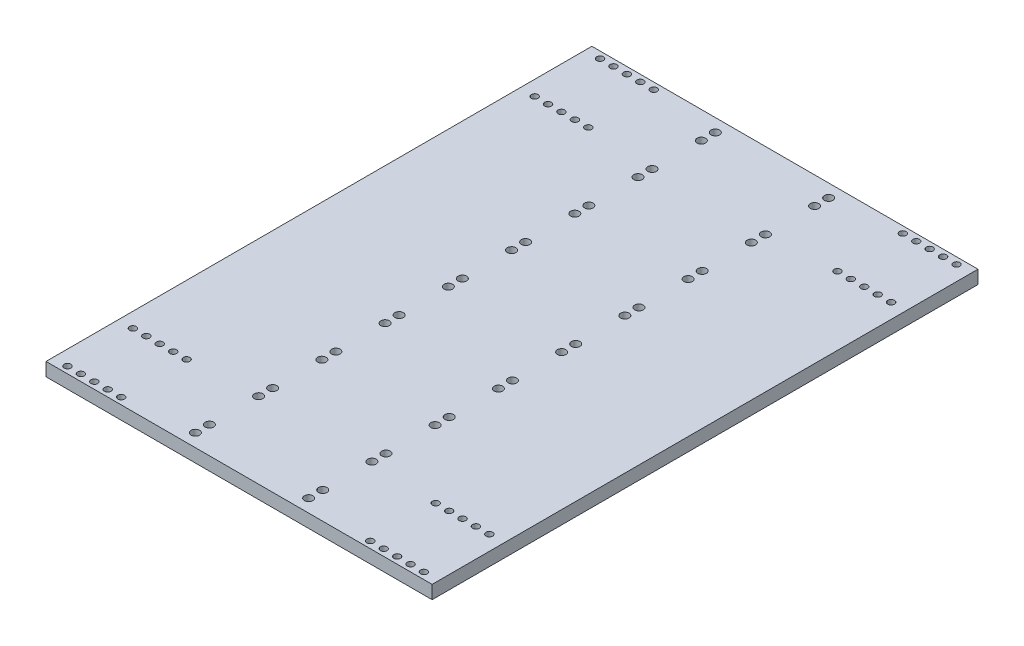
SolidWorks part; units mm, degrees
ref_plane "Front Plane" through (0, 0, 0) normal (0, 0, 1) x (1, 0, 0)
ref_plane "Top Plane" through (0, 0, 0) normal (0, 1, 0) x (1, 0, 0)
ref_plane "Right Plane" through (0, 0, 0) normal (1, 0, 0) x (0, 0, -1)
sketch "Sketch1" plane through (0, 0, 0) normal (0, 1, 0) x (1, 0, 0)
  line L1 (-92.075, 130.175) -> (92.075, 130.175)
  line L2 (-92.075, 130.175) -> (-92.075, -130.175)
  line L3 (-92.075, -130.175) -> (92.075, -130.175)
  line L4 (92.075, 130.175) -> (92.075, -130.175)
  line L5 (-92.075, 130.175) -> (92.075, -130.175) construction
  line L6 (-92.075, -130.175) -> (92.075, 130.175) construction
  point P0 (0, 0)
  dimension "D1" = 260.35
  dimension "D2" = 184.15
extrude "Boss-Extrude1" add sketch "Sketch1" against normal blind 6.35
sketch "Sketch2" plane through (0, 0, 0) normal (0, 1, 0) x (1, 0, 0)
  line L0 (0, 130.175) -> (0, -130.175) construction
  line L1 (92.075, 0) -> (-92.075, 0) construction
  line L2 (-27.0205, -117.2972) -> (27.0205, -117.2972)
  line L3 (-27.0205, -117.2972) -> (-27.0205, -124.0028)
  line L4 (92.075, -130.175) -> (92.075, 130.175)
  line L5 (92.075, 130.175) -> (-92.075, 130.175)
  line L6 (-92.075, 130.175) -> (-92.075, -130.175)
  line L7 (-92.075, -130.175) -> (92.075, -130.175)
  line L8 (92.075, -130.175) -> (92.075, 130.175)
  line L9 (92.075, 130.175) -> (-92.075, 130.175)
  line L10 (-92.075, 130.175) -> (-92.075, -130.175)
  line L11 (-92.075, -130.175) -> (92.075, -130.175)
  line L12 (-27.0205, -124.0028) -> (27.0205, -124.0028)
  line L13 (27.0205, -117.2972) -> (27.0205, -124.0028)
  line L14 (-27.0205, -117.2972) -> (27.0205, -124.0028) construction
  line L15 (-27.0205, -124.0028) -> (27.0205, -117.2972) construction
  line L16 (-27.0205, -87.1347) -> (-27.0205, -93.8403)
  line L17 (-27.0205, -87.1347) -> (27.0205, -87.1347)
  line L18 (27.0205, -87.1347) -> (27.0205, -93.8403)
  line L19 (-27.0205, -93.8403) -> (27.0205, -93.8403)
  line L20 (-27.0205, -56.9722) -> (-27.0205, -63.6778)
  line L21 (-27.0205, -56.9722) -> (27.0205, -56.9722)
  line L22 (27.0205, -56.9722) -> (27.0205, -63.6778)
  line L23 (-27.0205, -63.6778) -> (27.0205, -63.6778)
  line L24 (-27.0205, -26.8097) -> (-27.0205, -33.5153)
  line L25 (-27.0205, -26.8097) -> (27.0205, -26.8097)
  line L26 (27.0205, -26.8097) -> (27.0205, -33.5153)
  line L27 (-27.0205, -33.5153) -> (27.0205, -33.5153)
  line L28 (-27.0205, 3.3528) -> (-27.0205, -3.3528)
  line L29 (-27.0205, 3.3528) -> (27.0205, 3.3528)
  line L30 (27.0205, 3.3528) -> (27.0205, -3.3528)
  line L31 (-27.0205, -3.3528) -> (27.0205, -3.3528)
  line L32 (-27.0205, 33.5153) -> (-27.0205, 26.8097)
  line L33 (-27.0205, 33.5153) -> (27.0205, 33.5153)
  line L34 (27.0205, 33.5153) -> (27.0205, 26.8097)
  line L35 (-27.0205, 26.8097) -> (27.0205, 26.8097)
  line L36 (-27.0205, 63.6778) -> (-27.0205, 56.9722)
  line L37 (-27.0205, 63.6778) -> (27.0205, 63.6778)
  line L38 (27.0205, 63.6778) -> (27.0205, 56.9722)
  line L39 (-27.0205, 56.9722) -> (27.0205, 56.9722)
  line L40 (-27.0205, 93.8403) -> (-27.0205, 87.1347)
  line L41 (-27.0205, 93.8403) -> (27.0205, 93.8403)
  line L42 (27.0205, 93.8403) -> (27.0205, 87.1347)
  line L43 (-27.0205, 87.1347) -> (27.0205, 87.1347)
  line L44 (-27.0205, 124.0028) -> (-27.0205, 117.2972)
  line L45 (-27.0205, 124.0028) -> (27.0205, 124.0028)
  line L46 (27.0205, 124.0028) -> (27.0205, 117.2972)
  line L47 (-27.0205, 117.2972) -> (27.0205, 117.2972)
  circle A0 centre (-27.0205, -117.2972) radius 2.032
  circle A1 centre (-27.0205, -124.0028) radius 2.032
  circle A2 centre (27.0205, -124.0028) radius 2.032
  circle A3 centre (27.0205, -117.2972) radius 2.032
  circle A4 centre (-27.0205, -87.1347) radius 2.032
  circle A5 centre (-27.0205, -93.8403) radius 2.032
  circle A6 centre (27.0205, -87.1347) radius 2.032
  circle A7 centre (27.0205, -93.8403) radius 2.032
  circle A8 centre (-27.0205, -56.9722) radius 2.032
  circle A9 centre (-27.0205, -63.6778) radius 2.032
  circle A10 centre (27.0205, -56.9722) radius 2.032
  circle A11 centre (27.0205, -63.6778) radius 2.032
  circle A12 centre (-27.0205, -26.8097) radius 2.032
  circle A13 centre (-27.0205, -33.5153) radius 2.032
  circle A14 centre (27.0205, -26.8097) radius 2.032
  circle A15 centre (27.0205, -33.5153) radius 2.032
  circle A16 centre (-27.0205, 3.3528) radius 2.032
  circle A17 centre (-27.0205, -3.3528) radius 2.032
  circle A18 centre (27.0205, 3.3528) radius 2.032
  circle A19 centre (27.0205, -3.3528) radius 2.032
  circle A20 centre (-27.0205, 33.5153) radius 2.032
  circle A21 centre (-27.0205, 26.8097) radius 2.032
  circle A22 centre (27.0205, 33.5153) radius 2.032
  circle A23 centre (27.0205, 26.8097) radius 2.032
  circle A24 centre (-27.0205, 63.6778) radius 2.032
  circle A25 centre (-27.0205, 56.9722) radius 2.032
  circle A26 centre (27.0205, 63.6778) radius 2.032
  circle A27 centre (27.0205, 56.9722) radius 2.032
  circle A28 centre (-27.0205, 93.8403) radius 2.032
  circle A29 centre (-27.0205, 87.1347) radius 2.032
  circle A30 centre (27.0205, 93.8403) radius 2.032
  circle A31 centre (27.0205, 87.1347) radius 2.032
  circle A32 centre (-27.0205, 124.0028) radius 2.032
  circle A33 centre (-27.0205, 117.2972) radius 2.032
  circle A34 centre (27.0205, 124.0028) radius 2.032
  circle A35 centre (27.0205, 117.2972) radius 2.032
  point P6 (0, -120.65)
  dimension "D5" = 4.064
  dimension "D6" = 4.064
  dimension "D7" = 4.064
  dimension "D8" = 4.064
  dimension "D2" = 6.7056
  dimension "D3" = 54.041
  dimension "D4" = 6.1722
  dimension "D10" = 30.1625
  dimension "D1" = 0
  dimension "D9" = 9
extrude "Cut-Extrude1" cut sketch "Sketch2" against normal through all contours L44 A33 L47 | L46 A34 L45 | L45 A34 L46 | L47 A35 L46 | L46 A35 L47 | L40 A28 L41 | L41 A28 L40 | L43 A29 L40 | L40 A29 L43 | L41 A30 L42 | L42 A30 L41 | L42 A31 L43 | L43 A31 L42 | L45 A32 L44 | L44 A32 L45 | L47 A33 L44 | L37 A24 L36 | L36 A24 L37 | L39 A25 L36 | L36 A25 L39 | L37 A26 L38 | L38 A26 L37 | L38 A27 L39 | L39 A27 L38 | L33 A20 L32 | L32 A20 L33 | L35 A21 L32 | L32 A21 L35 | L33 A22 L34 | L34 A22 L33 | L34 A23 L35 | L35 A23 L34 | L28 A16 L29 | L29 A16 L28 | L31 A17 L28 | L28 A17 L31 | L29 A18 L30 | L30 A18 L29 | L30 A19 L31 | L31 A19 L30 | L25 A12 L24 | L24 A12 L25 | A13 | A14 | A15 | A8 | A9 | A10 | A11 | A4 | A5 | A6 | A7 | A3 | A0 | A1 | A2
sketch "Sketch3" plane through (0, 0, 0) normal (0, 1, 0) x (1, 0, 0)
  line L0 (92.075, 130.175) -> (-92.075, 130.175) construction
  line L1 (92.075, -130.175) -> (92.075, 130.175) construction
  line L2 (-92.075, 130.175) -> (-92.075, -130.175) construction
  line L3 (-92.075, -130.175) -> (92.075, -130.175) construction
  line L4 (92.075, 130.175) -> (-92.075, 130.175)
  line L5 (92.075, -130.175) -> (92.075, 130.175)
  line L6 (-92.075, 130.175) -> (-92.075, -130.175)
  line L7 (-92.075, -130.175) -> (92.075, -130.175)
  line L8 (0, -130.175) -> (0, 130.175) construction
  line L9 (-92.075, 0) -> (92.075, 0) construction
  circle A10 centre (-85.0055, -95.8) radius 1.6
  circle A11 centre (-85.0055, -127) radius 1.6
  circle A12 centre (-78.6055, -95.8) radius 1.6
  circle A13 centre (-78.6055, -127) radius 1.6
  circle A14 centre (-72.2055, -95.8) radius 1.6
  circle A15 centre (-72.2055, -127) radius 1.6
  circle A16 centre (-65.8055, -95.8) radius 1.6
  circle A17 centre (-59.4055, -95.8) radius 1.6
  circle A18 centre (-65.8055, -127) radius 1.6
  circle A19 centre (-59.4055, -127) radius 1.6
  circle A20 centre (-27.0205, -124.0028) radius 2.032 construction
  circle A21 centre (-27.0205, -124.0028) radius 2.032
  circle A22 centre (85.0055, -127) radius 1.6
  circle A23 centre (78.6055, -127) radius 1.6
  circle A24 centre (72.2055, -127) radius 1.6
  circle A25 centre (65.8055, -127) radius 1.6
  circle A26 centre (59.4055, -127) radius 1.6
  circle A27 centre (59.4055, -95.8) radius 1.6
  circle A28 centre (65.8055, -95.8) radius 1.6
  circle A29 centre (72.2055, -95.8) radius 1.6
  circle A30 centre (78.6055, -95.8) radius 1.6
  circle A31 centre (85.0055, -95.8) radius 1.6
  circle A32 centre (85.0055, 127) radius 1.6
  circle A33 centre (78.6055, 127) radius 1.6
  circle A34 centre (72.2055, 127) radius 1.6
  circle A35 centre (65.8055, 127) radius 1.6
  circle A36 centre (59.4055, 127) radius 1.6
  circle A37 centre (85.0055, 95.8) radius 1.6
  circle A38 centre (78.6055, 95.8) radius 1.6
  circle A39 centre (72.2055, 95.8) radius 1.6
  circle A40 centre (65.8055, 95.8) radius 1.6
  circle A41 centre (59.4055, 95.8) radius 1.6
  circle A42 centre (-59.4055, 127) radius 1.6
  circle A43 centre (-65.8055, 127) radius 1.6
  circle A44 centre (-72.2055, 127) radius 1.6
  circle A45 centre (-78.6055, 127) radius 1.6
  circle A46 centre (-85.0055, 127) radius 1.6
  circle A47 centre (-59.4055, 95.8) radius 1.6
  circle A48 centre (-65.8055, 95.8) radius 1.6
  circle A49 centre (-72.2055, 95.8) radius 1.6
  circle A50 centre (-78.6055, 95.8) radius 1.6
  circle A51 centre (-85.0055, 95.8) radius 1.6
  point P9 (85.0055, -95.8)
  point P10 (78.6055, -95.8)
  point P11 (72.2055, -95.8)
  point P12 (65.8055, -95.8)
  point P13 (59.4055, -95.8)
  point P14 (78.6055, -127)
  point P15 (72.2055, -127)
  point P18 (85.0055, -127)
  point P19 (59.4055, -127)
  point P62 (85.0055, 127)
  point P65 (78.6055, 127)
  point P68 (72.2055, 127)
  point P73 (59.4055, 127)
  point P76 (85.0055, 95.8)
  point P79 (78.6055, 95.8)
  point P82 (72.2055, 95.8)
  point P85 (65.8055, 95.8)
  point P88 (59.4055, 95.8)
  dimension "D3" = 31.2
  dimension "D5" = 31.2
  dimension "D24" = 3.2
  dimension "D25" = 3.2
  dimension "D26" = 3.2
  dimension "D27" = 3.2
  dimension "D28" = 3.2
  dimension "D31" = 3.2
  dimension "D32" = 3.2
  dimension "D33" = 3.2
  dimension "D34" = 3.2
  dimension "D35" = 3.2
  dimension "D4" = 31.2
  dimension "D6" = 31.2
  dimension "D10" = 6.4
  dimension "D11" = 6.4
  dimension "D12" = 6.4
  dimension "D13" = 6.4
  dimension "D16" = 6.4
  dimension "D17" = 6.4
  dimension "D18" = 6.4
  dimension "D19" = 6.4
  dimension "D22" = 31.2
  dimension "D36" = 32.385
  dimension "D37" = 3.175
extrude "Cut-Extrude2" cut sketch "Sketch3" against normal up to surface (6.35 mm away) contours A17 | A16 | A14 | A12 | A10 | A19 | A18 | A15 | A13 | A11 | A26 | A27 | A28 | A29 | A30 | A31 | A25 | A24 | A23 | A22 | A37 | A38 | A39 | A40 | A36 | A35 | A34 | A33 | A32 | A41 | A47 | A48 | A49 | A50 | A51 | A42 | A43 | A44 | A45 | A46 up to face at (-27.0205, -6.35, 35.5473)
